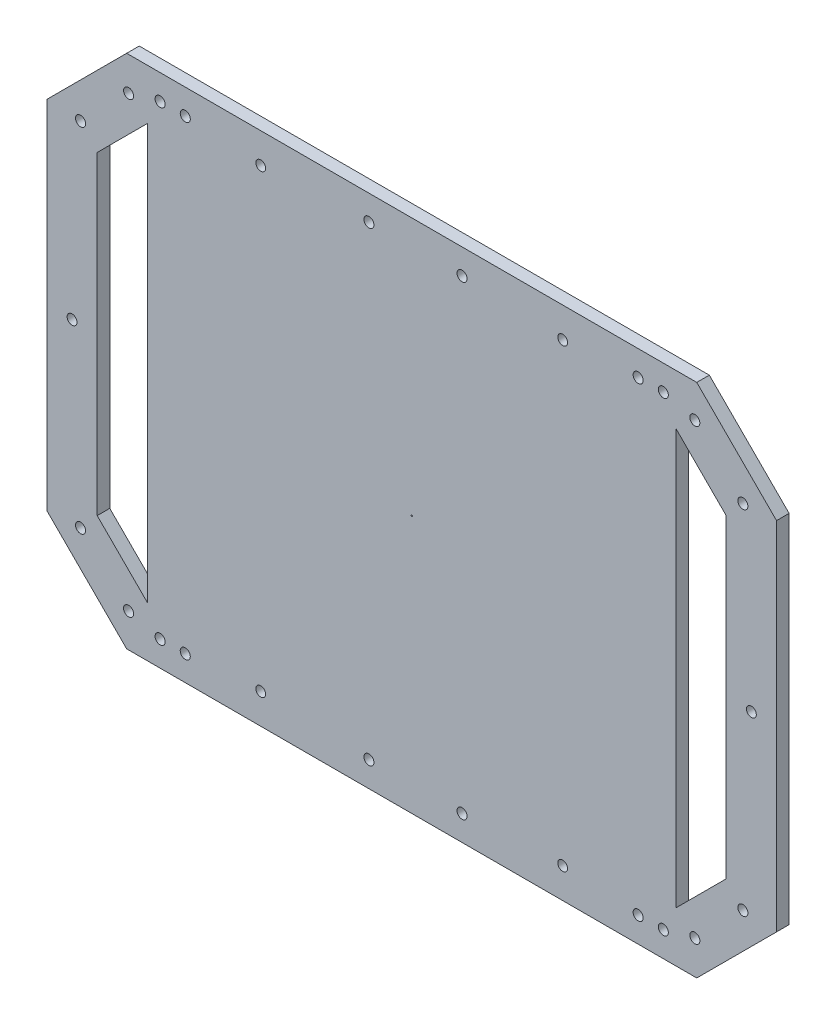
SolidWorks part; units mm, degrees
ref_plane "Front Plane" through (0, 0, 0) normal (0, 0, 1) x (1, 0, 0)
ref_plane "Top Plane" through (0, 0, 0) normal (0, 1, 0) x (1, 0, 0)
ref_plane "Right Plane" through (0, 0, 0) normal (1, 0, 0) x (0, 0, -1)
sketch "Sketch1" plane through (0, 0, 0) normal (0, 0, 1) x (1, 0, 0)
  line L0 (-95.9104, 67.5903) -> (114.0896, 67.5903)
  line L1 (134.0896, 47.5903) -> (134.0896, -77.4097)
  line L2 (114.0896, -97.4097) -> (-95.9104, -97.4097)
  line L3 (-115.9104, 47.5903) -> (-115.9104, -77.4097)
  line L4 (-115.9104, 47.5903) -> (-95.9104, 67.5903)
  line L5 (114.0896, 67.5903) -> (134.0896, 47.5903)
  line L6 (-95.9104, -97.4097) -> (-115.9104, -77.4097)
  line L7 (134.0896, -77.4097) -> (114.0896, -97.4097)
  line L8 (-104.1946, 87.5903) -> (122.3739, 87.5903)
  line L9 (122.3739, 87.5903) -> (154.0896, 55.8745)
  line L10 (154.0896, 55.8745) -> (154.0896, -85.694)
  line L11 (154.0896, -85.694) -> (122.3739, -117.4097)
  line L12 (122.3739, -117.4097) -> (-104.1946, -117.4097)
  line L13 (-104.1946, -117.4097) -> (-135.9104, -85.694)
  line L14 (-135.9104, 55.8745) -> (-135.9104, -85.694)
  line L15 (-135.9104, 55.8745) -> (-104.1946, 87.5903)
  line L16 (-95.9104, 67.5903) -> (-95.9104, -97.4097)
  line L17 (114.0896, 67.5903) -> (114.0896, -97.4097)
  circle A0 centre (121.6148, 74.2073) radius 2
  circle A1 centre (140.7067, 55.1154) radius 2
  circle A2 centre (-103.4355, 74.2073) radius 2
  circle A3 centre (-103.4355, -104.0267) radius 2
  circle A4 centre (-122.5274, 55.1154) radius 2
  circle A5 centre (-122.5274, -84.9349) radius 2
  circle A6 centre (121.6148, -104.0267) radius 2
  circle A7 centre (140.7067, -84.9349) radius 2
  circle A8 centre (29.0896, 77.5903) radius 2
  circle A9 centre (29.0896, -107.4097) radius 2
  circle A10 centre (-7.9104, -107.4097) radius 2
  circle A11 centre (-7.9104, 77.5903) radius 2
  circle A12 centre (-90.9104, 77.5903) radius 2
  circle A13 centre (109.0896, -107.4097) radius 2
  circle A14 centre (99.0896, -107.4097) radius 2
  circle A15 centre (-80.9104, 77.5903) radius 2
  circle A16 centre (-90.9104, -107.4097) radius 2
  circle A17 centre (-80.9104, -107.4097) radius 2
  circle A18 centre (99.0896, 77.5903) radius 2
  circle A19 centre (109.0896, 77.5903) radius 2
  circle A20 centre (69.0896, 75.5903) radius 1.95
  circle A21 centre (-50.9104, 75.5903) radius 1.95
  circle A22 centre (-50.9104, -105.4097) radius 1.95
  circle A23 centre (69.0896, -105.4097) radius 1.95
  circle A24 centre (144.0896, -14.9097) radius 1.95
  circle A25 centre (-125.9104, -14.9097) radius 1.95
  circle A26 centre (9.0896, -14.9097) radius 0.25
  point P0 (-115.9104, 67.5903)
  point P1 (134.0896, 67.5903)
  point P2 (134.0896, -97.4097)
  point P4 (-115.9104, -97.4097)
  point P20 (-105.9104, 57.5903)
  point P21 (-120.0525, 43.4481)
  point P22 (-91.7682, 71.7324)
  point P23 (-120.0525, 71.7324)
  point P24 (-105.9104, 85.8745)
  point P25 (-134.1946, 57.5903)
  point P26 (49.0896, 67.5903)
  point P27 (49.0896, 87.5903)
  point P28 (89.0896, 87.5903)
  point P29 (89.0896, 67.5903)
  point P30 (-30.9104, 67.5903)
  point P31 (-30.9104, 87.5903)
  point P32 (-105.9104, -87.4097)
  point P33 (-120.0525, -101.5519)
  point P34 (-120.0525, -73.2676)
  point P35 (-91.7682, -101.5519)
  point P36 (-105.9104, -115.694)
  point P37 (-134.1946, -87.4097)
  point P40 (-70.9104, 87.5903)
  point P41 (-70.9104, 67.5903)
  point P42 (-30.9104, -97.4097)
  point P43 (-30.9104, -117.4097)
  point P44 (124.0896, -87.4097)
  point P45 (138.2318, -101.5519)
  point P46 (109.9475, -101.5519)
  point P47 (138.2318, -73.2676)
  point P48 (152.3739, -87.4097)
  point P49 (124.0896, -115.694)
  point P50 (124.0896, -87.4097)
  point P51 (109.9475, -101.5519)
  point P54 (-70.9104, -97.4097)
  point P55 (-70.9104, -117.4097)
  point P56 (49.0896, -97.4097)
  point P57 (49.0896, -117.4097)
  point P58 (124.0896, 57.5903)
  point P59 (138.2318, 71.7324)
  point P60 (124.0896, 85.8745)
  point P61 (152.3739, 57.5903)
  point P62 (138.2318, 43.4481)
  point P63 (109.9475, 71.7324)
  point P66 (89.0896, -97.4097)
  point P67 (89.0896, -117.4097)
  point P68 (134.0896, -14.9097)
  point P69 (154.0896, -14.9097)
  point P86 (9.0896, 87.5903)
  point P87 (39.0896, 87.5903)
  point P88 (-17.9104, 87.5903)
  point P89 (-22.6883, 67.5903)
  point P90 (39.0896, 67.5903)
  point P93 (-115.9104, -14.9097)
  point P94 (-135.9104, -14.9097)
  point P95 (9.0896, -97.4097)
  point P96 (9.0896, -117.4097)
  point P97 (39.0896, -117.4097)
  point P98 (9.0896, 67.5903)
  point P99 (-17.9104, -117.4097)
  point P100 (-17.9104, -97.4097)
  point P101 (39.0896, -97.4097)
  point P102 (-134.4104, -14.9097)
  point P103 (152.5896, -14.9097)
  point P107 (9.0896, -14.9097)
  point P116 (-75.9104, 87.5903)
  point P117 (94.0896, 67.5903)
  point P118 (94.0896, 87.5903)
  point P120 (-75.9104, 67.5903)
  point P140 (-75.9104, -117.4097)
  point P141 (-75.9104, -97.4097)
  point P142 (94.0896, -97.4097)
  point P143 (94.0896, -117.4097)
  dimension "D29" = 4
  dimension "D54" = 4
  dimension "D67" = 4
  dimension "D33" = 4
  dimension "D34" = 4
  dimension "D37" = 4
  dimension "D40" = 4
  dimension "D44" = 4
  dimension "D58" = 4
  dimension "D61" = 4
  dimension "D70" = 4
  dimension "D74" = 4
  dimension "D82" = 4
  dimension "D86" = 4
  dimension "D88" = 4
  dimension "D89" = 4
  dimension "D90" = 4
  dimension "D91" = 4
  dimension "D92" = 4
  dimension "D93" = 4
  dimension "D94" = 4
  dimension "D95" = 4
  dimension "D100" = 3.9
  dimension "D106" = 3.9
  dimension "D112" = 3.9
  dimension "D118" = 3.9
  dimension "D122" = 3.9
  dimension "D124" = 3.9
  dimension "D126" = 0.5
  dimension "D2" = 210
  dimension "D3" = 20
  dimension "D4" = 45
  dimension "D5" = 20
  dimension "D6" = 45
  dimension "D7" = 20
  dimension "D8" = 45
  dimension "D9" = 20
  dimension "D10" = 45
  dimension "D11" = 20
  dimension "D12" = 125
  dimension "D13" = 20
  dimension "D14" = 20
  dimension "D15" = 20
  dimension "D16" = 20
  dimension "D17" = 20
  dimension "D18" = 20
  dimension "D19" = 20
  dimension "D20" = 20
  dimension "D21" = 20
  dimension "D22" = 20
  dimension "D23" = 20
  dimension "D24" = 20
  dimension "D25" = 20
  dimension "D26" = 20
  dimension "D27" = 20
  dimension "D28" = 20
  dimension "D30" = 226.5685
  dimension "D31" = 27
  dimension "D32" = 10
  dimension "D35" = 10
  dimension "D36" = 10
  dimension "D38" = 10
  dimension "D39" = 10
  dimension "D41" = 27
  dimension "D42" = 10
  dimension "D43" = 10
  dimension "D45" = 27
  dimension "D46" = 27
  dimension "D47" = 30
  dimension "D48" = 116.7779
  dimension "D49" = 30
  dimension "D50" = 27
  dimension "D51" = 30
  dimension "D52" = 27
  dimension "D53" = 30
  dimension "D55" = 10
  dimension "D56" = 10
  dimension "D57" = 37
  dimension "D59" = 10
  dimension "D60" = 10
  dimension "D62" = 37
  dimension "D63" = 85
  dimension "D64" = 85
  dimension "D65" = 85
  dimension "D66" = 85
  dimension "D68" = 10
  dimension "D69" = 10
  dimension "D71" = 10
  dimension "D72" = 10
  dimension "D73" = 10
  dimension "D75" = 10
  dimension "D76" = 85
  dimension "D77" = 85
  dimension "D78" = 85
  dimension "D79" = 85
  dimension "D80" = 10
  dimension "D81" = 10
  dimension "D83" = 10
  dimension "D84" = 10
  dimension "D85" = 10
  dimension "D87" = 10
  dimension "D96" = 40
  dimension "D97" = 40
  dimension "D98" = 40
  dimension "D99" = 40
  dimension "D101" = 8
  dimension "D102" = 40
  dimension "D103" = 40
  dimension "D104" = 40
  dimension "D105" = 40
  dimension "D107" = 8
  dimension "D108" = 40
  dimension "D109" = 40
  dimension "D110" = 40
  dimension "D111" = 40
  dimension "D113" = 8
  dimension "D114" = 40
  dimension "D115" = 40
  dimension "D116" = 40
  dimension "D117" = 40
  dimension "D119" = 1.5
  dimension "D120" = 8
  dimension "D121" = 1.5
  dimension "D123" = 10
  dimension "D125" = 10
extrude "Boss-Extrude1" add sketch "Sketch1" along normal blind 5 contours L17 L0 L16 L2 | L15 L14 L13 L12 L11 L10 L9 L8 A19 A18 A17 A16 A15 A14 A13 A12 A11 A10 A9 A8 A7 A6 A5 A4 A3 A2 A1 A0 L1 L7
